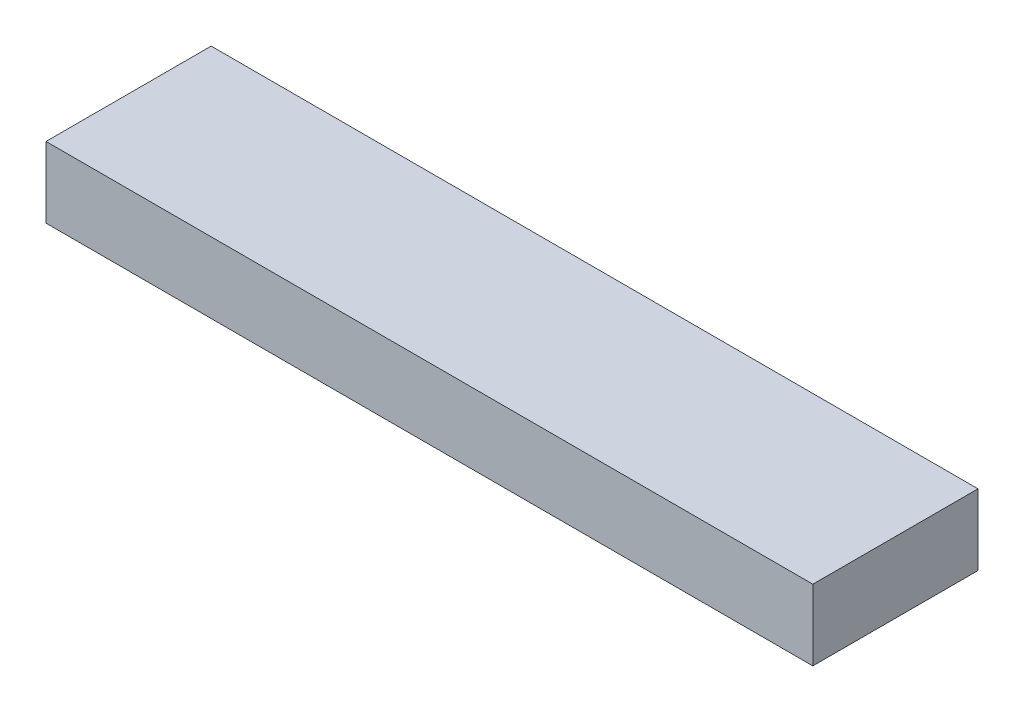
SolidWorks part; units mm, degrees
ref_plane "Front Plane" through (0, 0, 0) normal (0, 0, 1) x (1, 0, 0)
ref_plane "Top Plane" through (0, 0, 0) normal (0, 1, 0) x (1, 0, 0)
ref_plane "Right Plane" through (0, 0, 0) normal (1, 0, 0) x (0, 0, -1)
sketch "Sketch1" plane through (0, 0, 0) normal (0, 1, 0) x (1, 0, 0)
  line L1 (0, 0) -> (412.75, 0)
  line L2 (0, 0) -> (0, -88.9)
  line L3 (0, -88.9) -> (412.75, -88.9)
  line L4 (412.75, 0) -> (412.75, -88.9)
extrude "Boss-Extrude1" add sketch "Sketch1" along normal blind 38.1
sketch "Sketch2" plane through (0, 38.1, 0) normal (0, 1, 0) x (1, 0, 0)
  line L0 (0, -44.45) -> (137.5833, -44.45) construction
  line L1 (0, 0) -> (0, -88.9) construction
  line L2 (137.5833, -44.45) -> (275.1667, -44.45) construction
  line L3 (275.1667, -44.45) -> (412.75, -44.45) construction
  line L4 (412.75, -88.9) -> (412.75, 0) construction
  line L5 (137.5833, 0) -> (137.5833, -88.9) construction
  line L6 (412.75, 0) -> (0, 0) construction
  line L7 (0, -88.9) -> (412.75, -88.9) construction
  line L8 (275.1667, 0) -> (275.1667, -88.9) construction
sketch "Sketch3" plane through (0, 0, 0) normal (0, -1, 0) x (1, 0, 0)
  line L0 (0, 44.45) -> (137.5833, 44.45) construction
  line L1 (137.5833, 44.45) -> (275.1667, 44.45) construction
  line L2 (275.1667, 44.45) -> (412.75, 44.45) construction
  line L3 (137.5833, 88.9) -> (137.5833, 0) construction
  line L4 (275.1667, 88.9) -> (275.1667, 0) construction
